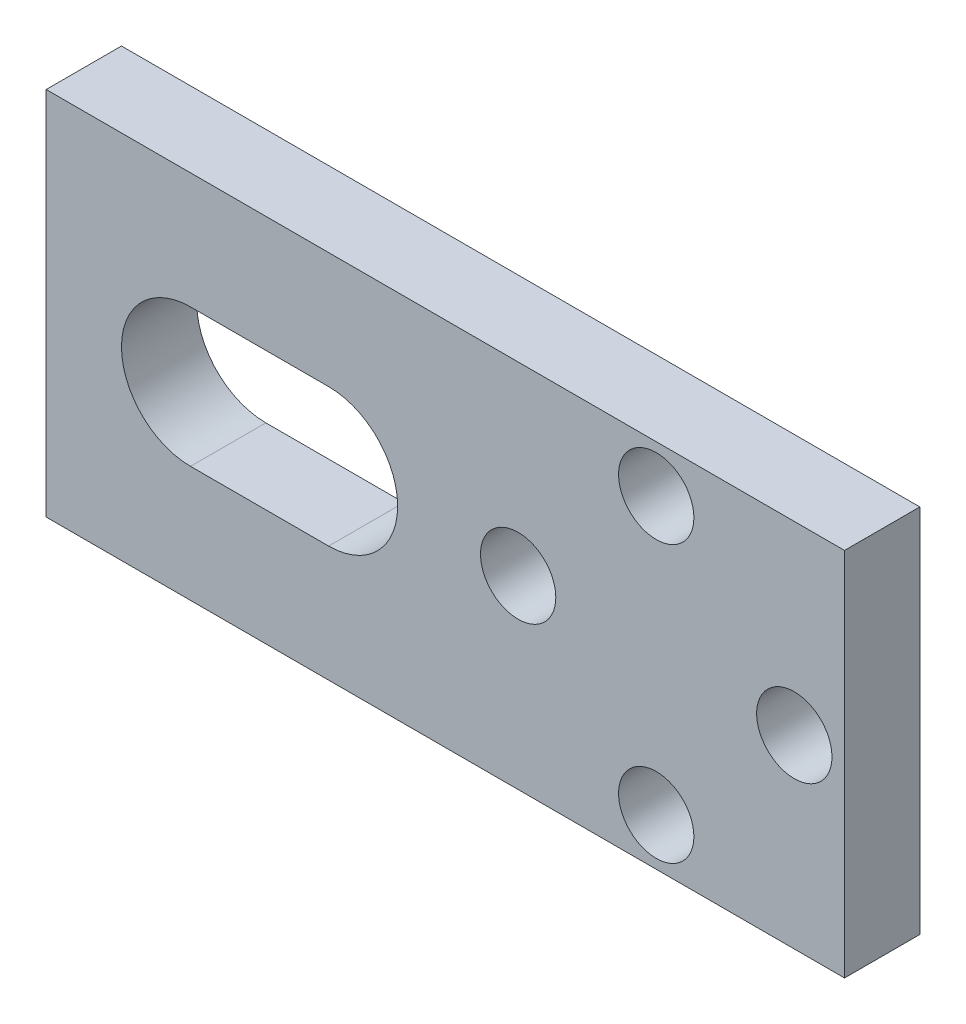
SolidWorks part; units mm, degrees
ref_plane "Front Plane" through (0, 0, 0) normal (0, 0, 1) x (1, 0, 0)
ref_plane "Top Plane" through (0, 0, 0) normal (0, 1, 0) x (1, 0, 0)
ref_plane "Right Plane" through (0, 0, 0) normal (1, 0, 0) x (0, 0, -1)
sketch "Sketch1" plane through (0, 0, 0) normal (0, 0, 1) x (1, 0, 0)
  line L0 (0, 7.375) -> (31.8, 7.375) construction
  line L1 (0, 0) -> (31.8, 0)
  line L2 (0, 0) -> (0, 14.75)
  line L3 (0, 14.75) -> (31.8, 14.75)
  line L4 (31.8, 0) -> (31.8, 14.75)
  line L5 (5.75, 7.375) -> (11.25, 7.375) construction
  line L6 (5.75, 10.125) -> (11.25, 10.125)
  line L7 (5.75, 4.625) -> (11.25, 4.625)
  line L8 (24.3, 14.75) -> (24.3, 0) construction
  arc A0 (5.75, 10.125) -> (5.75, 4.625) centre (5.75, 7.375) ccw
  arc A1 (11.25, 4.625) -> (11.25, 10.125) centre (11.25, 7.375) ccw
  circle A2 centre (29.8, 7.375) radius 1.5
  circle A3 centre (18.8, 7.375) radius 1.5
  circle A4 centre (24.3, 12.875) radius 1.5
  circle A5 centre (24.3, 1.875) radius 1.5
  point P9 (8.5, 7.375)
  dimension "D6" = 3
  dimension "D1" = 31.8
  dimension "D2" = 14.75
  dimension "D3" = 5.5
  dimension "D4" = 5.5
  dimension "D5" = 5.75
  dimension "D7" = 5.5
  dimension "D8" = 5.5
  dimension "D9" = 2
  dimension "D10" = 11
  dimension "D11" = 5.5
extrude "Boss-Extrude1" add sketch "Sketch1" along normal blind 3
